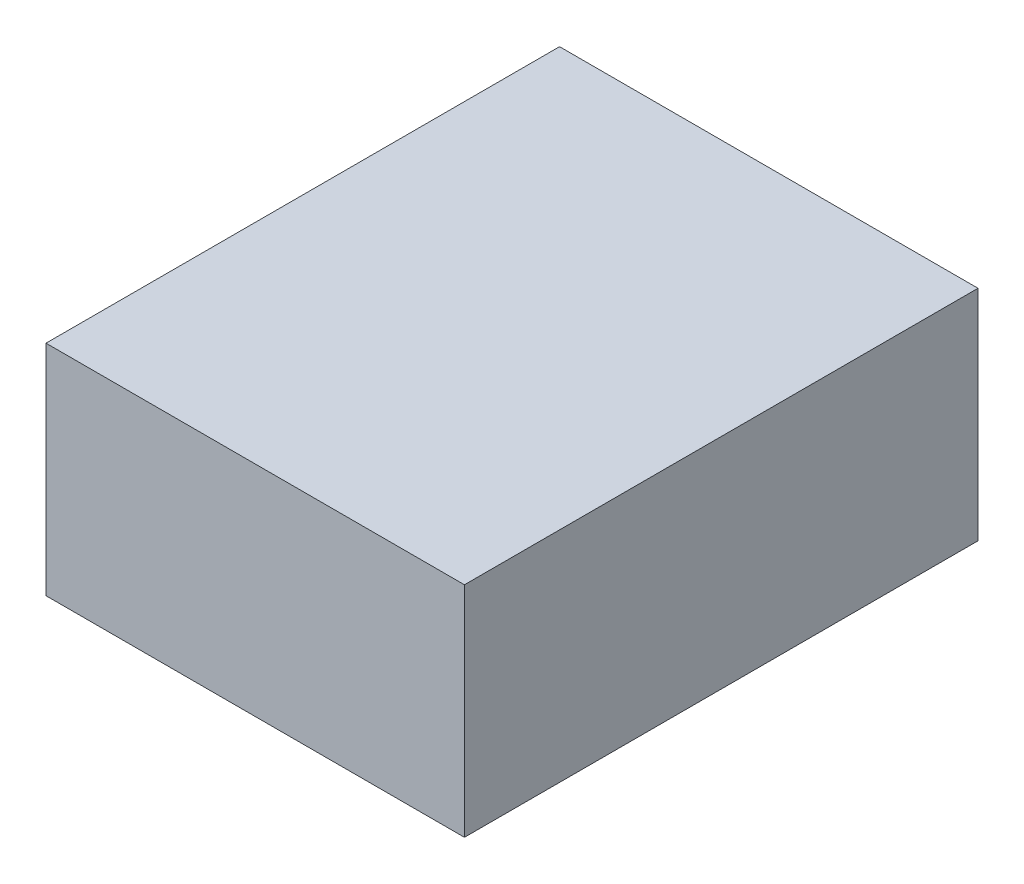
SolidWorks part; units mm, degrees
ref_plane "正面" through (0, 0, 0) normal (0, 0, 1) x (1, 0, 0)
ref_plane "平面" through (0, 0, 0) normal (0, 1, 0) x (1, 0, 0)
ref_plane "右側面" through (0, 0, 0) normal (1, 0, 0) x (0, 0, -1)
sketch "ｽｹｯﾁ1" plane through (0, 0, 0) normal (0, 0, 1) x (1, 0, 0)
  line L1 (-40.0594, 20.5411) -> (-18.0594, 20.5411)
  line L2 (-40.0594, 20.5411) -> (-40.0594, 9.0411)
  line L3 (-40.0594, 9.0411) -> (-18.0594, 9.0411)
  line L4 (-18.0594, 20.5411) -> (-18.0594, 9.0411)
  dimension "D1" = 22
  dimension "D2" = 11.5
extrude "ﾎﾞｽ - 押し出し1" add sketch "ｽｹｯﾁ1" along normal blind 27
